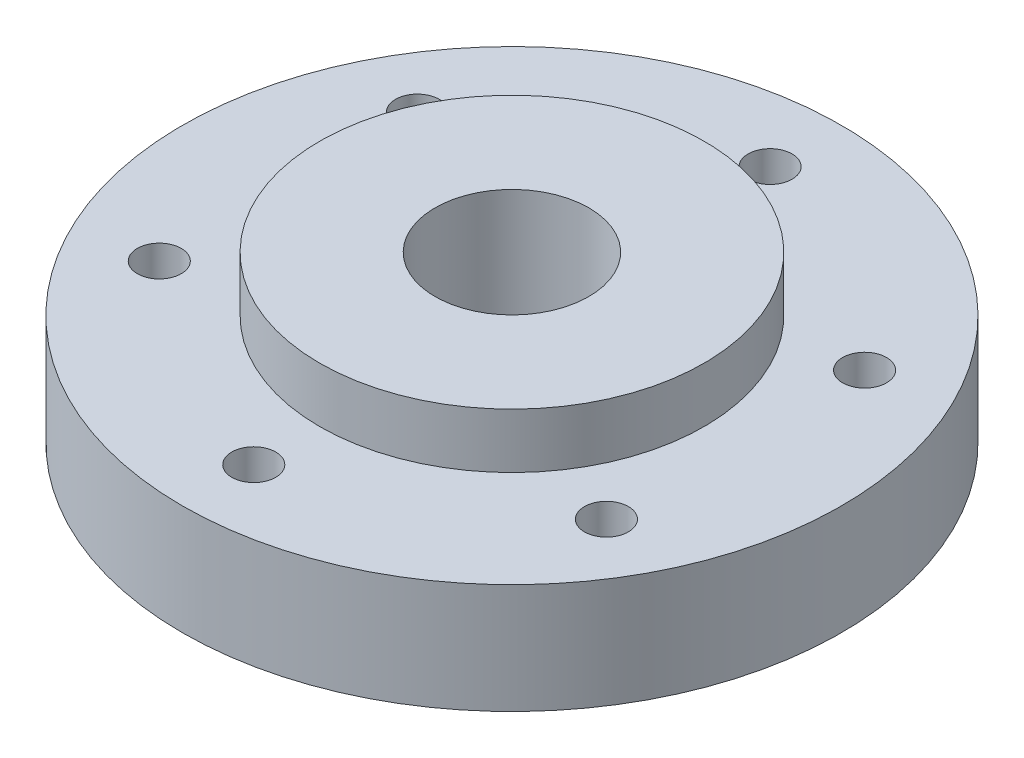
SolidWorks part; units mm, degrees
material "ABS"
ref_plane "Front Plane" through (0, 0, 0) normal (0, 0, 1) x (1, 0, 0)
ref_plane "Top Plane" through (0, 0, 0) normal (0, 1, 0) x (1, 0, 0)
ref_plane "Right Plane" through (0, 0, 0) normal (1, 0, 0) x (0, 0, -1)
sketch "Sketch1" plane through (0, 0, 0) normal (0, 1, 0) x (1, 0, 0)
  circle A0 centre (0, 0) radius 30
  dimension "D1" = 60
extrude "Boss-Extrude1" add sketch "Sketch1" along normal blind 15
sketch "Sketch3" plane through (0, 0, 0) normal (0, -1, 0) x (1, 0, 0)
  circle A0 centre (0, 0) radius 16.25
  dimension "D1" = 32.5
extrude "Cut-Extrude1" cut sketch "Sketch3" against normal blind 5
sketch "Sketch4" plane through (0, 5, 0) normal (0, -1, 0) x (1, 0, 0)
  circle A0 centre (0, 0) radius 7
  dimension "D1" = 14
extrude "Cut-Extrude2" cut sketch "Sketch4" against normal through all
sketch "Sketch5" plane through (0, 15, 0) normal (0, 1, 0) x (1, 0, 0)
  circle A0 centre (0, 0) radius 17.5
  circle A1 centre (0, 0) radius 30 construction
  circle A2 centre (0, 0) radius 30
  dimension "D1" = 35
extrude "Cut-Extrude3" cut sketch "Sketch5" against normal blind 5
sketch "Sketch6" plane through (0, 10, 0) normal (0, 1, 0) x (1, 0, 0)
  circle A0 centre (0, 0) radius 23.5 construction
  circle A1 centre (0, 23.5) radius 2
  circle A2 centre (20.3516, 11.75) radius 2
  circle A3 centre (20.3516, -11.75) radius 2
  circle A4 centre (0, -23.5) radius 2
  circle A5 centre (-20.3516, -11.75) radius 2
  circle A6 centre (-20.3516, 11.75) radius 2
  point P17 (0, 0)
  dimension "D1" = 47
  dimension "D2" = 4
  dimension "D3" = 6
extrude "Cut-Extrude4" cut sketch "Sketch6" against normal through all
